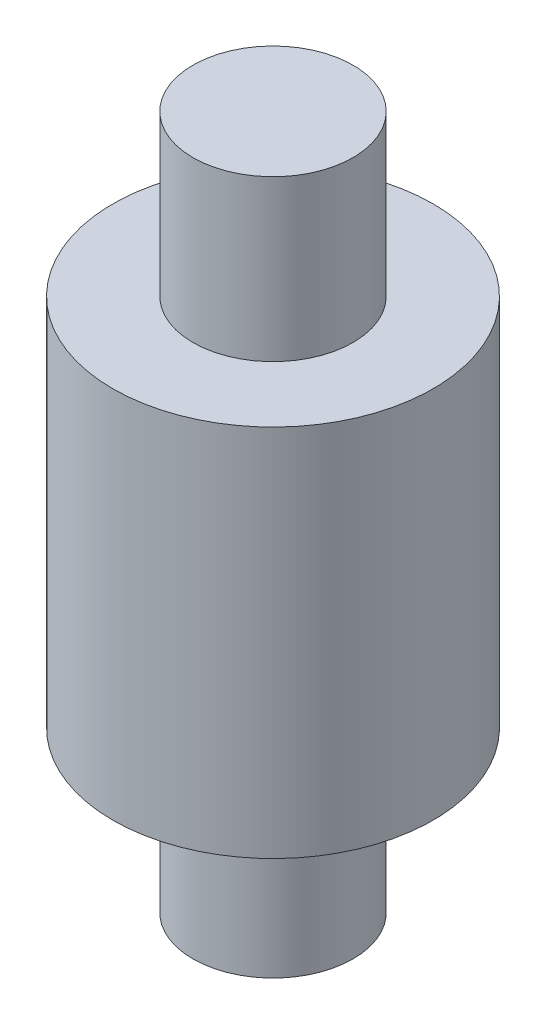
SolidWorks part; units mm, degrees
ref_plane "Спереди" through (0, 0, 0) normal (0, 0, 1) x (1, 0, 0)
ref_plane "Сверху" through (0, 0, 0) normal (0, 1, 0) x (1, 0, 0)
ref_plane "Справа" through (0, 0, 0) normal (1, 0, 0) x (0, 0, -1)
sketch "Эскиз1" plane through (0, 0, 0) normal (0, 1, 0) x (1, 0, 0)
  circle A0 centre (0, 0) radius 3
  dimension "D1" = 6
extrude "Бобышка-Вытянуть1" add sketch "Эскиз1" along normal blind 7
sketch "Эскиз2" plane through (0, 0, 0) normal (0, -1, 0) x (1, 0, 0)
  circle A0 centre (0, 0) radius 1.5
  dimension "D1" = 3
extrude "Бобышка-Вытянуть2" add sketch "Эскиз2" along normal blind 3
sketch "Эскиз3" plane through (0, 7, 0) normal (0, 1, 0) x (1, 0, 0)
  circle A0 centre (0, 0) radius 1.5
  dimension "D1" = 3
extrude "Бобышка-Вытянуть3" add sketch "Эскиз3" along normal blind 3
